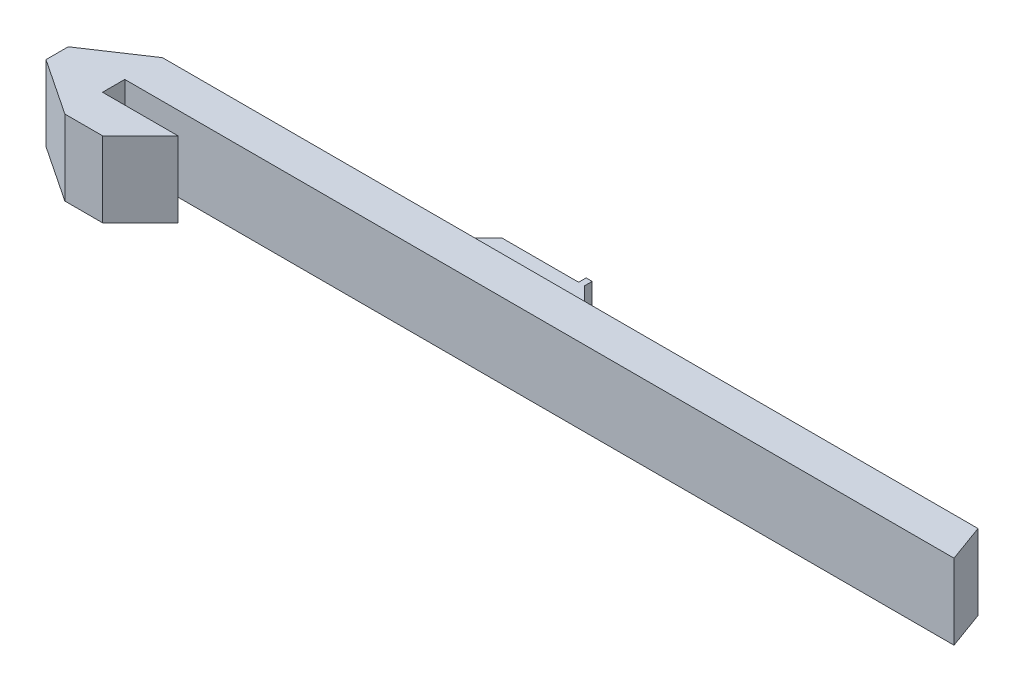
SolidWorks part; units mm, degrees
ref_plane "Ebene vorne" through (0, 0, 0) normal (0, 0, 1) x (1, 0, 0)
ref_plane "Ebene oben" through (0, 0, 0) normal (0, 1, 0) x (1, 0, 0)
ref_plane "Ebene rechts" through (0, 0, 0) normal (1, 0, 0) x (0, 0, -1)
sketch "Skizze1" plane through (0, 0, 0) normal (0, 1, 0) x (1, 0, 0)
  line L0 (0, 0) -> (220, 0)
  line L2 (216.3603, 10) -> (0, 10)
  line L3 (0, 10) -> (-15, 0)
  line L6 (10, -15.9) -> (20, -5.9)
  line L7 (20, -5.9) -> (0, -5.9)
  line L8 (0, -5.9) -> (0, 0)
  line L9 (-15, 0) -> (-15, -5.9)
  line L10 (-15, -5.9) -> (0, -15.9)
  line L11 (0, -15.9) -> (10, -15.9)
  line L12 (70, 10) -> (80, 20)
  line L13 (80, 20) -> (102, 20)
  line L14 (102, 20) -> (112, 10)
  line L15 (70, 10) -> (112, 10)
  line L16 (-15, 0) -> (0, 0)
  line L17 (-15, -5.9) -> (0, -5.9)
  line L18 (0, -5.9) -> (0, -15.9)
  line L19 (0, 10) -> (0, 0)
  line L20 (80, 20) -> (80, 0)
  line L21 (216.3603, 10) -> (220, 0)
  dimension "D1" = 5.9
  dimension "D2" = 10
  dimension "D3" = 10
  dimension "D4" = 15
  dimension "D5" = 20
  dimension "D6" = 220
  dimension "D7" = 22
  dimension "D8" = 10
  dimension "D9" = 45
  dimension "D10" = 45
  dimension "D11" = 45
  dimension "D12" = 70
  dimension "D13" = 80
extrude "Aufsatz-Linear austragen1" add sketch "Skizze1" along normal blind 20 contours L7 L18 L11 L6 | L18 L17 L10 | L9 L17 L8 L16 | L19 L3 L16 | L20 L15 L2 L19 L0 | L21 L2 L20 L0 | L13 L20 L2 L14 | L20 L12 L15
sketch "Skizze2" plane through (0, 20, 0) normal (0, 1, 0) x (1, 0, 0)
  line L0 (70, 10) -> (112, 10)
  line L1 (112, 10) -> (102, 20)
  line L2 (102, 20) -> (80, 20)
  line L3 (80, 20) -> (70, 10)
extrude "Schnitt-Linear austragen1" cut sketch "Skizze2" against normal blind 6.4
sketch "Skizze3" plane through (0, 0, 0) normal (0, -1, 0) x (1, 0, 0)
  line L0 (70, -10) -> (112, -10)
  line L1 (112, -10) -> (102, -20)
  line L2 (102, -20) -> (80, -20)
  line L3 (80, -20) -> (70, -10)
extrude "Schnitt-Linear austragen2" cut sketch "Skizze3" against normal blind 6.4
sketch "Skizze4" plane through (0, 0, -20) normal (0, 0, -1) x (-1, 0, 0)
  line L0 (-80, 6.4) -> (-102, 6.4) construction
  line L1 (-102, 13.6) -> (-100.4, 13.6)
  line L2 (-102, 13.6) -> (-102, 6.4)
  line L3 (-102, 6.4) -> (-100.4, 6.4)
  line L4 (-100.4, 13.6) -> (-100.4, 6.4)
  dimension "D1" = 1.6
extrude "Aufsatz-Linear austragen2" add sketch "Skizze4" along normal blind 2
